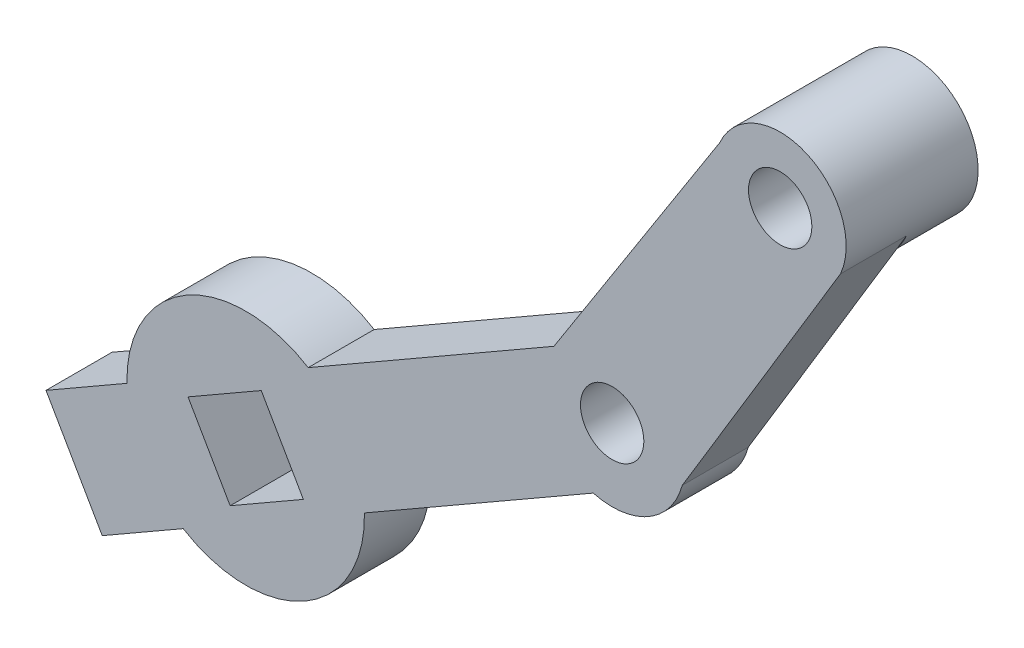
SolidWorks part; units mm, degrees
ref_plane "Front Plane" through (0, 0, 0) normal (0, 0, 1) x (1, 0, 0)
ref_plane "Top Plane" through (0, 0, 0) normal (0, 1, 0) x (1, 0, 0)
ref_plane "Right Plane" through (0, 0, 0) normal (1, 0, 0) x (0, 0, -1)
sketch "Sketch1" plane through (0, 0, 0) normal (0, 0, 1) x (0.4985, -0.8669, 0)
  line L0 (4.6263, -46.838) -> (4.6263, -41.838) construction
  line L2 (8.8991, 3.8691) -> (-2.3564, 24.18)
  line L3 (1.121, -3.909) -> (-10.421, 18.2671)
  line L4 (-2.3564, 24.18) -> (-10.421, 18.2671) construction
  line L6 (0.3536, -46.838) -> (8.8991, -46.838)
  line L7 (0.3536, -46.838) -> (0.3536, -2.4346)
  line L9 (8.8991, -46.838) -> (8.8991, -3.909)
  circle A0 centre (5.01, -0.02) radius 2.5 construction
  arc A1 (1.121, -3.909) -> (8.8991, 3.8691) centre (5.01, -0.02) ccw
  arc A2 (-2.3564, 24.18) -> (-10.421, 18.2671) centre (-6.3887, 21.2235) ccw
  circle A3 centre (-6.3887, 21.2235) radius 2 construction
  circle A5 centre (5.01, -0.02) radius 5.5 construction
  point P16 (10.01, -0.02)
  dimension "D2" = 4
  dimension "D3" = 5
  dimension "D5" = 5
  dimension "D4" = 25
  dimension "D6" = 42.929
  dimension "D7" = 8.5456
  dimension "D8" = 10
  dimension "D1" = 3
extrude "Boss-Extrude1" add sketch "Sketch1" along normal blind 5 contours L2 A2 L3 A1 A3 A0 | A1 L3 L7 L6 L9
sketch "Sketch8" plane through (0, 0, 0) normal (0, 0, -1) x (-1, 0, 0)
  line L0 (38.2963, -27.3606) -> (25.2932, -19.8826) construction
  line L1 (23.2692, -23.6476) -> (36.1662, -31.0645) construction
  line L2 (25.3993, -19.9436) -> (23.2692, -23.6476) construction
  line L3 (38.2963, -27.3606) -> (36.1662, -31.0645) construction
  line L4 (36.1662, -31.0645) -> (-1.0478, -9.6632) construction
  circle A0 centre (25.2932, -19.8826) radius 9
  dimension "D1" = 18
  dimension "D3" = 4.2728
  dimension "D2" = 15
  dimension "D4" = 14.8776
extrude "Boss-Extrude3" add sketch "Sketch8" against normal up to surface (5 mm away) up to face at (-5.2053, -5.1823, 5)
ref_plane "Plane1" through (2.3064, -4.0104, 0) normal (0.4985, -0.8669, 0) x (-0.8669, -0.4985, 0)
sketch "Sketch3" plane through (0, 0, 0) normal (0, 0, -1) x (-1, 0, 0)
  line L0 (36.092, -21.164) -> (18.7546, -11.1934) construction
  line L1 (36.1662, -31.0645) -> (40.4264, -23.6566) construction
  line L2 (40.4264, -23.6566) -> (18.7546, -11.1934) construction
  line L3 (40.4264, -23.6566) -> (1.9342, -1.5202) construction
  line L4 (18.7546, -11.1934) -> (14.4943, -18.6013) construction
  line L5 (36.1662, -31.0645) -> (-1.0478, -9.6632) construction
  line L6 (14.4943, -18.6013) -> (36.1662, -31.0645) construction
  line L7 (36.1662, -31.0645) -> (40.4264, -23.6566)
  line L8 (36.1662, -31.0645) -> (31.8318, -28.5719)
  line L9 (40.4264, -23.6566) -> (36.092, -21.164)
  line L10 (31.8318, -28.5719) -> (36.092, -21.164)
  line L11 (14.4943, -18.6013) -> (18.7546, -11.1934)
  line L12 (14.4943, -18.6013) -> (10.16, -16.1087)
  line L13 (18.7546, -11.1934) -> (14.4202, -8.7007)
  line L14 (10.16, -16.1087) -> (14.4202, -8.7007)
  dimension "D1" = 20
  dimension "D2" = 5
  dimension "D3" = 5
sketch "Sketch11" plane through (0, 0, 0) normal (0, 0, -1) x (-1, 0, 0)
  line L0 (26.4719, -24.2519) -> (29.6625, -18.7039)
  line L1 (26.4719, -24.2519) -> (20.9239, -21.0613)
  line L2 (29.6625, -18.7039) -> (24.1145, -15.5133)
  line L3 (20.9239, -21.0613) -> (24.1145, -15.5133)
  line L4 (26.4719, -24.2519) -> (24.1145, -15.5133) construction
  line L5 (29.6625, -18.7039) -> (20.9239, -21.0613) construction
  line L6 (40.4264, -23.6566) -> (36.1662, -31.0645) construction
  point P1 (25.2932, -19.8826)
  dimension "D1" = 6.4
  dimension "D2" = 6.4
extrude "Cut-Extrude1" cut sketch "Sketch11" against normal up to next
sketch "Sketch12" plane through (-24.8256, -14.2769, 0) normal (-0.8669, -0.4985, 0) x (0, 0, 1)
  line L0 (5, -4.6263) -> (0, -4.6263) construction
  line L1 (5, -1.4263) -> (5, -7.8263) construction
  line L2 (0, -1.4263) -> (0, -7.8263) construction
  line L3 (5, -7.8263) -> (5, -1.4263) construction
  circle A0 centre (2.5, -4.6263) radius 1
  point P13 (5, -4.6263)
  dimension "D1" = 2
extrude "Cut-Extrude2" cut sketch "Sketch12" against normal blind 0.5
sketch "Sketch13" plane through (0, 0, 0) normal (0, 0, -1) x (-1, 0, 0)
  circle A0 centre (-15.2132, 16.1188) radius 2 construction
  circle A1 centre (-15.2132, 16.1188) radius 5
  dimension "D1" = 10
  dimension "D2" = 4
extrude "Boss-Extrude5" add sketch "Sketch13" along normal blind 5
sketch "Sketch15" plane through (0, 0, -5) normal (0, 0, -1) x (-1, 0, 0)
  circle A0 centre (-15.2132, 16.1188) radius 2.4
extrude "Cut-Extrude3" cut sketch "Sketch15" against normal up to next
sketch "Sketch16" plane through (0, 0, 0) normal (0, 0, -1) x (-1, 0, 0)
  circle A0 centre (-2.4803, -4.353) radius 2.4
extrude "Cut-Extrude4" cut sketch "Sketch16" against normal up to next contours A0
